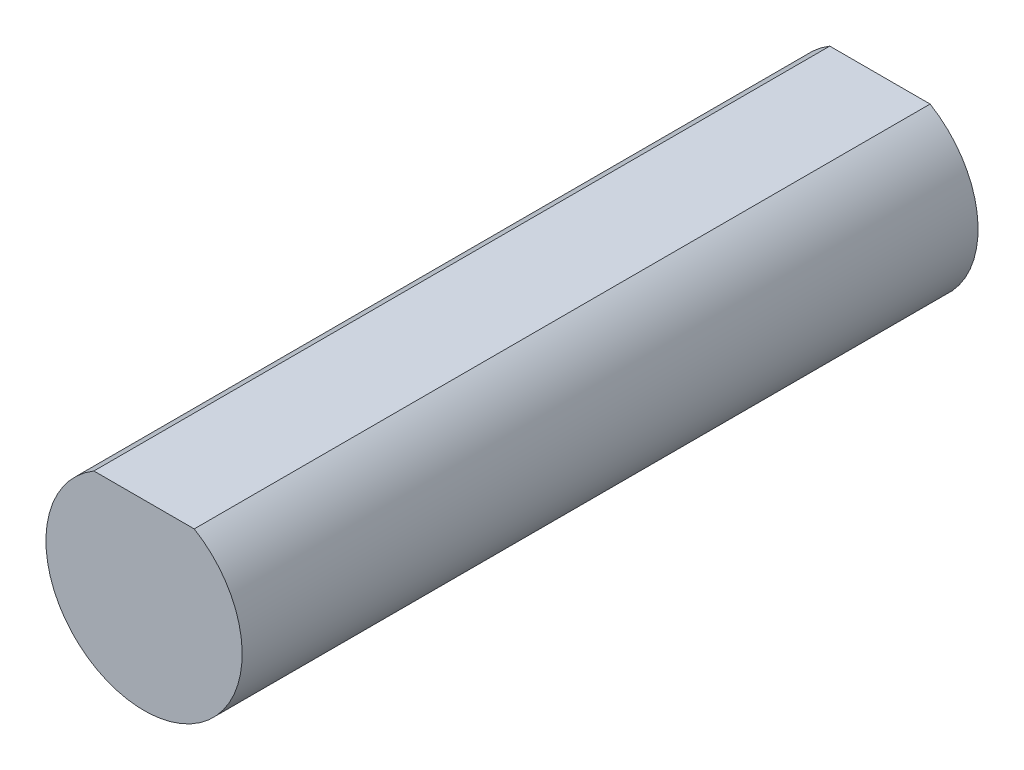
SolidWorks part; units mm, degrees
ref_plane "Front Plane" through (0, 0, 0) normal (0, 0, 1) x (1, 0, 0)
ref_plane "Top Plane" through (0, 0, 0) normal (0, 1, 0) x (1, 0, 0)
ref_plane "Right Plane" through (0, 0, 0) normal (1, 0, 0) x (0, 0, -1)
sketch "Sketch1" plane through (0, 0, 0) normal (0, 0, 1) x (1, 0, 0)
  line L0 (0, 0) -> (0, 1.7188) construction
  line L1 (-1.0227, 1.7188) -> (1.0227, 1.7188)
  arc A0 (-1.0227, 1.7188) -> (1.0227, 1.7188) centre (0, 0) ccw
  point P6 (0, 1.7188)
  dimension "D1" = 2
  dimension "D2" = 2.0453
extrude "Boss-Extrude1" add sketch "Sketch1" along normal blind 15
